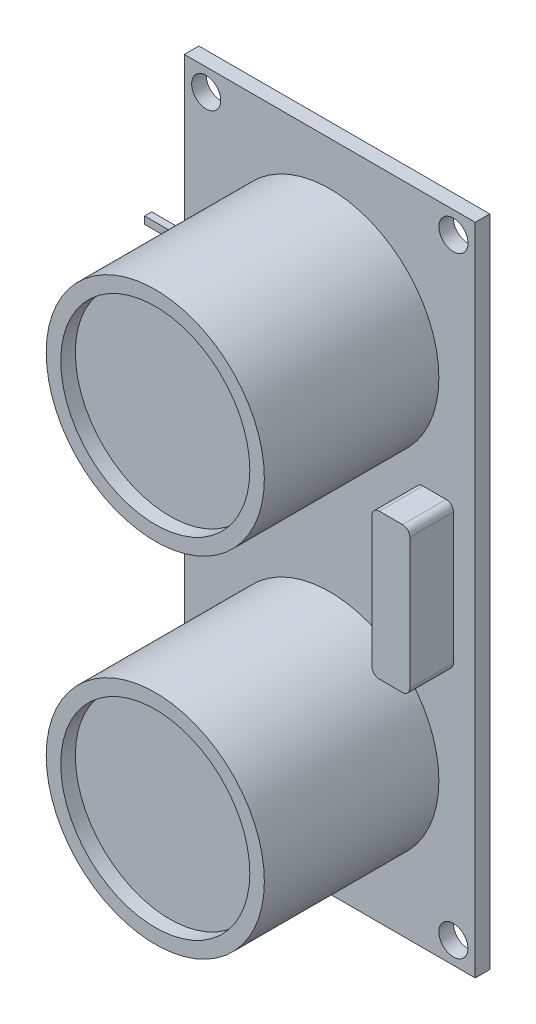
SolidWorks part; units mm, degrees
ref_plane "Front Plane" through (0, 0, 0) normal (0, 0, 1) x (1, 0, 0)
ref_plane "Top Plane" through (0, 0, 0) normal (0, 1, 0) x (1, 0, 0)
ref_plane "Right Plane" through (0, 0, 0) normal (1, 0, 0) x (0, 0, -1)
sketch "Sketch1" plane through (0, 0, 0) normal (0, 0, 1) x (1, 0, 0)
  line L1 (-2.2922, -57.3827) -> (-22.2922, -57.3827)
  line L2 (-2.2922, -57.3827) -> (-2.2922, -102.3827)
  line L3 (-2.2922, -102.3827) -> (-22.2922, -102.3827)
  line L4 (-22.2922, -57.3827) -> (-22.2922, -102.3827)
  dimension "D1" = 45
  dimension "D2" = 20
extrude "Boss-Extrude1" add sketch "Sketch1" along normal blind 1
sketch "Sketch2" plane through (0, 0, 1) normal (0, 0, 1) x (1, 0, 0)
  line L0 (-22.2922, -79.8827) -> (-2.2922, -79.8827) construction
  line L1 (-22.2922, -57.3827) -> (-22.2922, -102.3827) construction
  line L2 (-2.2922, -102.3827) -> (-2.2922, -57.3827) construction
  circle A0 centre (-12.2922, -67.8827) radius 7.5
  circle A1 centre (-12.2922, -91.8827) radius 7.5
  dimension "D1" = 15
  dimension "D2" = 15
  dimension "D3" = 12
  dimension "D4" = 12
extrude "Boss-Extrude2" add sketch "Sketch2" along normal blind 12
sketch "Sketch3" plane through (0, 0, 13) normal (0, 0, 1) x (1, 0, 0)
  circle A2 centre (-12.2922, -67.8827) radius 6.5
  circle A3 centre (-12.2922, -67.8827) radius 6.5
  circle A5 centre (-12.2922, -91.8827) radius 6.5
  circle A6 centre (-12.2922, -91.8827) radius 6.5
  dimension "D1" = 1
  dimension "D2" = 1
extrude "Cut-Extrude1" cut sketch "Sketch3" against normal blind 1
sketch "Sketch4" plane through (0, 0, 1) normal (0, 0, 1) x (1, 0, 0)
  line L0 (-22.2922, -79.8827) -> (-2.2922, -79.8827) construction
  line L1 (-22.2922, -57.3827) -> (-22.2922, -102.3827) construction
  line L2 (-2.2922, -102.3827) -> (-2.2922, -57.3827) construction
  line L4 (-6.3922, -74.8827) -> (-3.7922, -74.8827)
  line L5 (-6.3922, -74.8827) -> (-6.3922, -84.8827)
  line L6 (-6.3922, -84.8827) -> (-3.7922, -84.8827)
  line L7 (-3.7922, -74.8827) -> (-3.7922, -84.8827)
  dimension "D1" = 10
  dimension "D2" = 5
  dimension "D3" = 2.6
  dimension "D4" = 1.5
extrude "Boss-Extrude3" add sketch "Sketch4" along normal blind 3
fillet "Fillet1" radius 0.5 4 edges at (-6.3922, -74.8827, 2.5) (-3.7922, -74.8827, 2.5) (-6.3922, -84.8827, 2.5) (-3.7922, -84.8827, 2.5)
sketch "Sketch5" plane through (0, 0, 0) normal (0, 0, -1) x (-1, 0, 0)
  line L0 (22.2922, -79.8827) -> (2.2922, -79.8827) construction
  line L1 (20.7922, -87.3827) -> (17.7922, -87.3827)
  line L2 (20.7922, -87.3827) -> (20.7922, -72.3827)
  line L3 (20.7922, -72.3827) -> (17.7922, -72.3827)
  line L4 (17.7922, -87.3827) -> (17.7922, -72.3827)
  line L5 (22.2922, -57.3827) -> (22.2922, -102.3827) construction
  line L6 (2.2922, -102.3827) -> (2.2922, -57.3827) construction
  dimension "D1" = 15
  dimension "D2" = 7.5
  dimension "D3" = 3
  dimension "D4" = 1.5
extrude "Boss-Extrude4" add sketch "Sketch5" along normal blind 3
sketch "Sketch6" plane through (0, 0, -3) normal (0, 0, -1) x (-1, 0, 0)
  line L0 (19.2922, -87.3827) -> (19.2922, -72.3827) construction
  line L1 (19.5422, -84.8827) -> (19.0422, -84.8827)
  line L2 (19.5422, -84.8827) -> (19.5422, -84.3827)
  line L3 (19.5422, -84.3827) -> (19.0422, -84.3827)
  line L4 (19.0422, -84.8827) -> (19.0422, -84.3827)
  line L5 (19.5422, -81.8827) -> (19.0422, -81.8827)
  line L6 (19.5422, -81.8827) -> (19.5422, -81.3827)
  line L7 (19.5422, -81.3827) -> (19.0422, -81.3827)
  line L8 (19.0422, -81.8827) -> (19.0422, -81.3827)
  line L9 (19.5422, -78.3827) -> (19.0422, -78.3827)
  line L10 (19.5422, -78.3827) -> (19.5422, -77.8827)
  line L11 (19.5422, -77.8827) -> (19.0422, -77.8827)
  line L12 (19.0422, -78.3827) -> (19.0422, -77.8827)
  line L13 (19.5422, -75.3827) -> (19.0422, -75.3827)
  line L14 (19.5422, -75.3827) -> (19.5422, -74.8827)
  line L15 (19.5422, -74.8827) -> (19.0422, -74.8827)
  line L16 (19.0422, -75.3827) -> (19.0422, -74.8827)
  line L17 (17.7922, -87.3827) -> (20.7922, -87.3827) construction
  line L18 (20.7922, -72.3827) -> (17.7922, -72.3827) construction
  point P22 (19.5422, -75.1327)
  dimension "D1" = 0.5
  dimension "D2" = 0.5
  dimension "D3" = 0.5
  dimension "D4" = 0.5
  dimension "D5" = 0.5
  dimension "D6" = 0.5
  dimension "D7" = 0.5
  dimension "D8" = 0.5
  dimension "D9" = 0.25
  dimension "D10" = 0.25
  dimension "D11" = 0.25
  dimension "D12" = 0.25
  dimension "D13" = 2.5
  dimension "D14" = 2.5
  dimension "D15" = 2.5
  dimension "D16" = 2.5
extrude "Boss-Extrude5" add sketch "Sketch6" along normal blind 3
sketch "Sketch7" plane through (-19.5422, 0, 0) normal (-1, 0, 0) x (0, 0, 1)
  line L0 (-6, -75.3827) -> (-3, -75.3827) construction
  line L1 (-6, -74.8827) -> (-5.51, -74.8827)
  line L2 (-6, -74.8827) -> (-6, -75.3827)
  line L3 (-6, -75.3827) -> (-5.51, -75.3827)
  line L4 (-5.51, -74.8827) -> (-5.51, -75.3827)
  line L5 (-6, -78.3827) -> (-3, -78.3827) construction
  line L6 (-6, -77.8827) -> (-5.51, -77.8827)
  line L7 (-6, -77.8827) -> (-6, -78.3827)
  line L8 (-6, -78.3827) -> (-5.51, -78.3827)
  line L9 (-5.51, -77.8827) -> (-5.51, -78.3827)
  line L10 (-6, -81.8827) -> (-3, -81.8827) construction
  line L11 (-6, -81.3827) -> (-5.51, -81.3827)
  line L12 (-6, -81.3827) -> (-6, -81.8827)
  line L13 (-6, -81.8827) -> (-5.51, -81.8827)
  line L14 (-5.51, -81.3827) -> (-5.51, -81.8827)
  line L15 (-6, -84.8827) -> (-3, -84.8827) construction
  line L16 (-6, -84.3827) -> (-5.51, -84.3827)
  line L17 (-6, -84.3827) -> (-6, -84.8827)
  line L18 (-6, -84.8827) -> (-5.51, -84.8827)
  line L19 (-5.51, -84.3827) -> (-5.51, -84.8827)
extrude "Boss-Extrude6" add sketch "Sketch7" along normal blind 12
sketch "Sketch8" plane through (0, 0, 1) normal (0, 0, 1) x (1, 0, 0)
  line L0 (-22.2922, -79.8827) -> (-2.2922, -79.8827) construction
  line L1 (-22.2922, -57.3827) -> (-22.2922, -102.3827) construction
  line L2 (-2.2922, -102.3827) -> (-2.2922, -57.3827) construction
  line L3 (-12.2922, -57.3827) -> (-12.2922, -102.3827) construction
  line L4 (-2.2922, -57.3827) -> (-22.2922, -57.3827) construction
  line L5 (-22.2922, -102.3827) -> (-2.2922, -102.3827) construction
  circle A0 centre (-20.7922, -58.8827) radius 1
  circle A1 centre (-3.7922, -58.8827) radius 1
  circle A2 centre (-3.7922, -100.8827) radius 1
  circle A3 centre (-20.7922, -100.8827) radius 1
  dimension "D1" = 2
  dimension "D2" = 21
  dimension "D3" = 8.5
extrude "Cut-Extrude2" cut sketch "Sketch8" against normal blind 3
